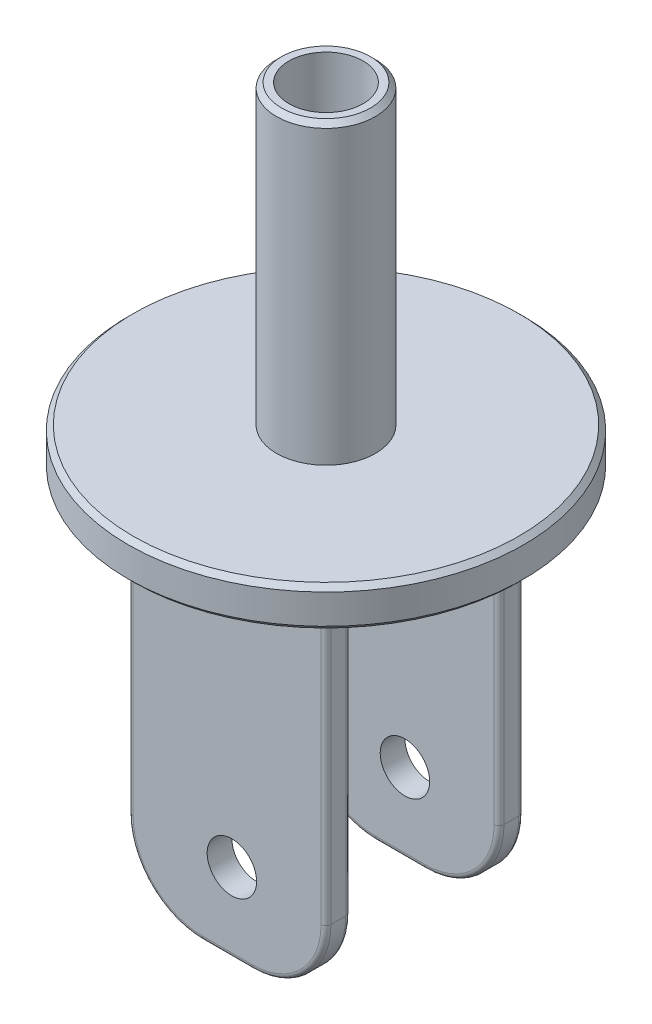
SolidWorks part; units mm, degrees
ref_plane "Front Plane" through (0, 0, 0) normal (0, 0, 1) x (1, 0, 0)
ref_plane "Top Plane" through (0, 0, 0) normal (0, 1, 0) x (1, 0, 0)
ref_plane "Right Plane" through (0, 0, 0) normal (1, 0, 0) x (0, 0, -1)
sketch "Sketch2" plane through (0, 0, 0) normal (0, 1, 0) x (1, 0, 0)
  circle A0 centre (0, 0) radius 40
  dimension "D1" = 80
extrude "Boss-Extrude1" add sketch "Sketch2" along normal blind 8
sketch "Sketch3" plane through (0, 0, 0) normal (0, -1, 0) x (1, 0, 0)
  line L0 (0, 0) -> (0, -17.5) construction
  line L2 (20, -20) -> (-20, -20)
  line L3 (20, -20) -> (20, -15)
  line L4 (20, -15) -> (-20, -15)
  line L5 (-20, -20) -> (-20, -15)
  line L6 (20, -20) -> (-20, -15) construction
  line L7 (20, -15) -> (-20, -20) construction
  point P7 (-20, -17.5)
  dimension "D1" = 15
  dimension "D2" = 40
  dimension "D3" = 2.5
extrude "Boss-Extrude2" add sketch "Sketch3" along normal blind 75
fillet "Fillet1" radius 15 2 edges at (20, -75, -17.5) (-20, -75, -17.5)
fillet "Fillet3" radius 1 10 edges at (20, -30, -20) (-20, -30, -20) (0, -75, -20) (15.6066, -70.6066, -20) (-15.6066, -70.6066, -20) (-20, -30, -15) (20, -30, -15) (15.6066, -70.6066, -15) (0, -75, -15) (-15.6066, -70.6066, -15)
fillet "Fillet4" radius 4 8 edges at (19.7071, 0, -15.2929) (20, 0, -17.5) (19.7071, 0, -19.7071) (0, 0, -20) (-19.7071, 0, -19.7071) (-20, 0, -17.5) (-19.7071, 0, -15.2929) (0, 0, -15)
mirror "Mirror10" about plane through (0, 0, 0) normal (0, 0, 1) of "Boss-Extrude2", "Fillet3", "Fillet1", "Fillet4"
sketch "Sketch5" plane through (0, 0, -20) normal (0, 0, -1) x (-1, 0, 0)
  line L0 (4.0384, -59) -> (-5.9616, -59) construction
  line L1 (-5, -74) -> (5, -74) construction
  circle A0 centre (-0.9616, -59) radius 5
  point P6 (0, -74)
  dimension "D2" = 10
  dimension "D1" = 10
  dimension "D3" = 15
extrude "Cut-Extrude1" cut sketch "Sketch5" against normal up to surface (40 mm away) contours A0 up to face at (0, -46.9665, 20)
sketch "Sketch6" plane through (0, 8, 0) normal (0, 1, 0) x (1, 0, 0)
  circle A0 centre (0, 0) radius 10
  dimension "D1" = 20
extrude "Boss-Extrude3" add sketch "Sketch6" along normal blind 60
sketch "Sketch7" plane through (0, 68, 0) normal (0, 1, 0) x (1, 0, 0)
  circle A0 centre (0, 0) radius 7.5
  dimension "D1" = 15
extrude "Cut-Extrude2" cut sketch "Sketch7" against normal blind 60
chamfer "Chamfer1" distance 1 angle 45 3 edges at (0, 0, 40) (0, 8, 40) (0, 68, 10)
sketch3d "3DSketch1"
  point P0 (26.6146, 0, -5.2846)
sketch3d "3DSketch2"
  point P0 (-6.6249, -25.8927, -20)
sketch3d "3DSketch3"
  point P0 (1.2925, -33.9757, 20)
